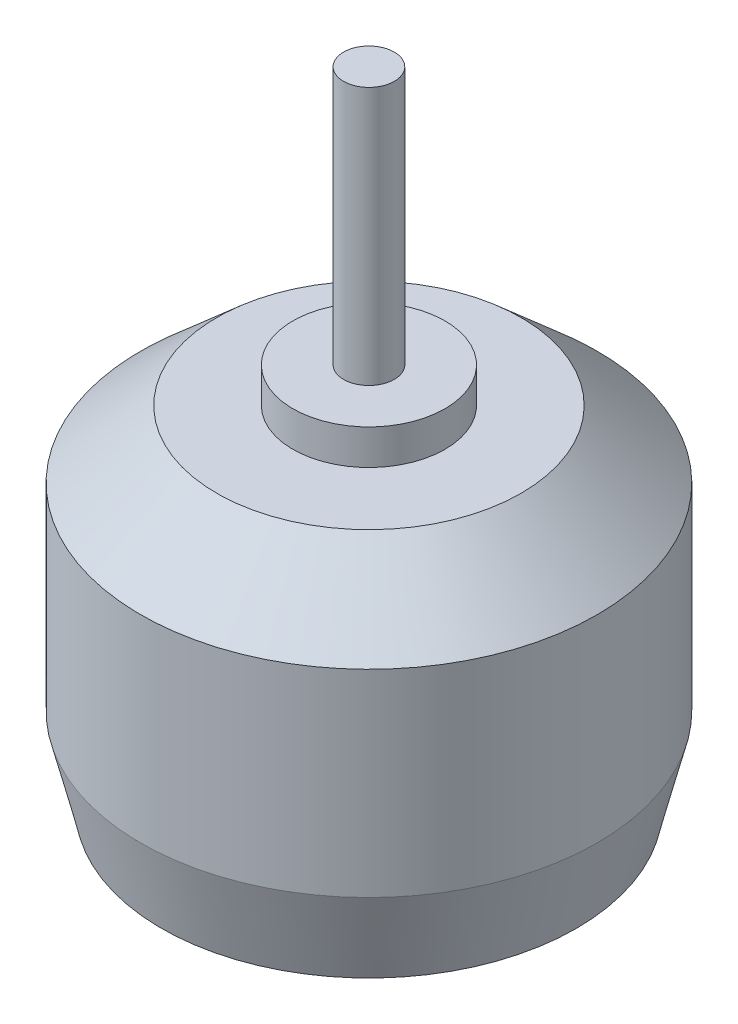
SolidWorks part; units mm, degrees
ref_plane "Alzado" through (0, 0, 0) normal (0, 0, 1) x (1, 0, 0)
ref_plane "Planta" through (0, 0, 0) normal (0, 1, 0) x (1, 0, 0)
ref_plane "Vista lateral" through (0, 0, 0) normal (1, 0, 0) x (0, 0, -1)
sketch "Croquis2" plane through (0, 0, 0) normal (0, 0, 1) x (1, 0, 0)
  line L0 (0, 19) -> (-1.5, 19)
  line L1 (-1.5, 19) -> (-1.5, 3.7341)
  line L2 (-1.5, 3.7341) -> (-4.5, 3.7341)
  line L3 (-4.5, 3.7341) -> (-4.5, 1.6548)
  line L4 (-4.5, 1.6548) -> (-9, 1.6548)
  line L5 (-9, 1.6548) -> (-13.5, -2.3138)
  line L6 (-13.5, -2.3138) -> (-13.5, -14)
  line L7 (-13.5, -14) -> (-12.2641, -19)
  line L8 (-12.2641, -19) -> (0, -19)
  line L9 (0, -19) -> (0, 19)
  point P2 (0, 0)
  point P11 (-30.1561, 5.0114)
  point P12 (-30.1561, 4.8871)
  point P13 (-14.7, 26.0504)
  point P14 (0, 46.0786)
  point P15 (-6, 25.871)
  point P16 (-14.7, 24.7703)
  point P18 (-14.7, 28.3872)
  point P19 (-30.1561, 8.0512)
  point P20 (-20.7945, -46.0786)
  point P21 (-30.1561, -19)
  point P22 (-11.4152, -19)
  point P23 (-14.7, 1.3086)
  point P24 (-14.7, 1.3086)
  point P25 (-14, 1.9057)
  point P26 (-14.7, 1.3086)
  point P27 (0, 0)
  point P28 (-12.4612, 1.2965)
  point P29 (-13.9188, -1.7645)
  point P30 (1.9205, 5.0863)
  point P31 (-0.8975, 19)
  point P32 (-13.5, -4.0481)
  point P33 (-15.1, 1.5394)
  point P34 (-13.5, -4.1452)
  point P35 (-10.4205, -19)
  point P36 (0, 0)
  point P37 (-13.5, -0.7927)
  point P38 (-14.8, 1.1021)
  point P39 (-13.06, 1.7248)
  point P40 (-9.9942, 1.6548)
  point P41 (-11.0335, 0.5461)
  point P42 (0, 0)
  dimension "D1" = 13.5
  dimension "D2" = 9
  dimension "D3" = 4.5
  dimension "D4" = 6
  dimension "D5" = 1.5
  dimension "D6" = 5
  dimension "D7" = 12.2641
  dimension "D8" = 38
  dimension "D9" = 20.6548
  dimension "D10" = 22.7341
revolve "Revolución1" add sketch "Croquis2" angle 360 about L9
sketch "Croquis3" plane through (0, -19, 0) normal (0, 1, 0) x (1, 0, 0)
  line L0 (0, -12.2641) -> (0, 12.2641) construction
  line L5 (-12.2641, 0) -> (12.2641, 0) construction
  circle A1 centre (0, 0) radius 12.2641 construction
  circle A2 centre (-9, 0) radius 1.25
  circle A3 centre (9, 0) radius 1.25
  circle A4 centre (0, -7) radius 1.25
  circle A5 centre (0, 7) radius 1.25
  point P0 (0, 0)
  dimension "D1" = 2.5
  dimension "D3" = 2.5
  dimension "D2" = 9
  dimension "D4" = 7
extrude "Cortar-Extruir1" cut sketch "Croquis3" against normal mid plane 10
